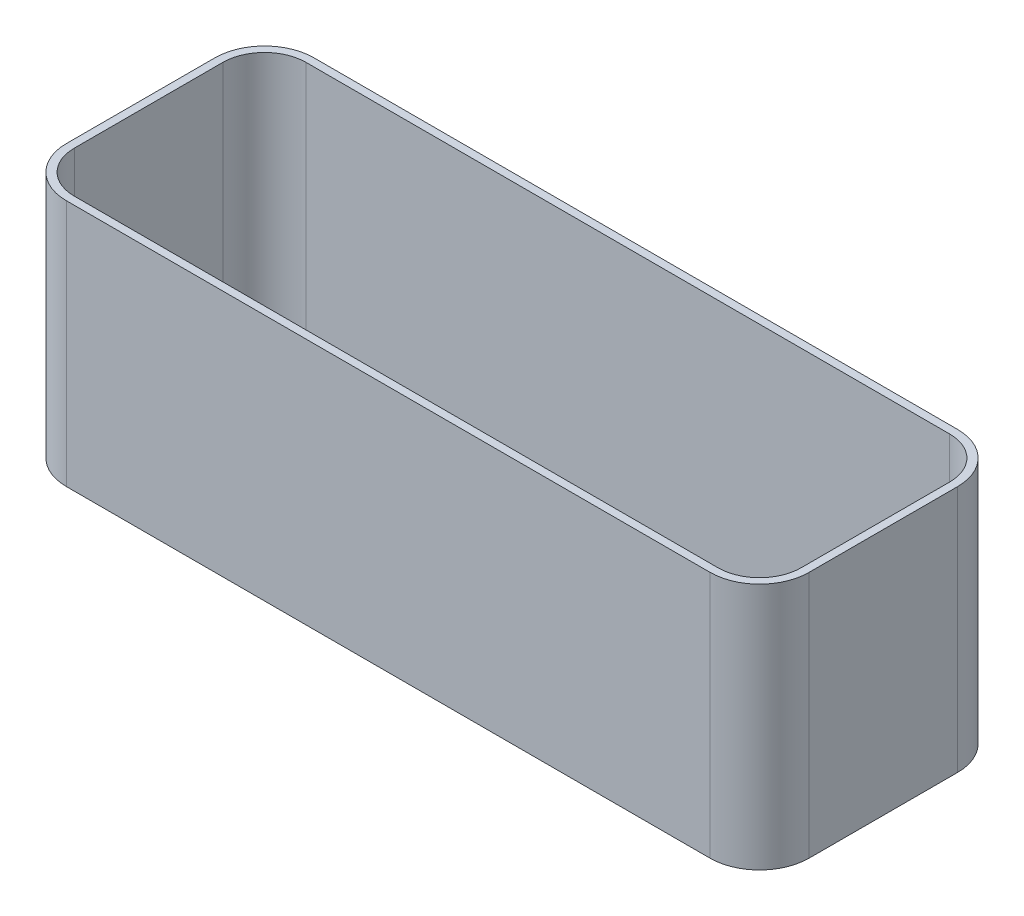
SolidWorks part; units mm, degrees
ref_plane "前视基准面" through (0, 0, 0) normal (0, 0, 1) x (1, 0, 0)
ref_plane "上视基准面" through (0, 0, 0) normal (0, 1, 0) x (1, 0, 0)
ref_plane "右视基准面" through (0, 0, 0) normal (1, 0, 0) x (0, 0, -1)
sketch "草图1" plane through (0, 0, 0) normal (0, 1, 0) x (1, 0, 0)
  line L1 (10, 0) -> (140, 0)
  line L2 (0, 10) -> (0, 40)
  line L3 (10, 50) -> (140, 50)
  line L4 (150, 10) -> (150, 40)
  arc A0 (150, 40) -> (140, 50) centre (140, 40) ccw
  arc A1 (140, 0) -> (150, 10) centre (140, 10) ccw
  arc A2 (10, 0) -> (0, 10) centre (10, 10) cw
  arc A3 (0, 40) -> (10, 50) centre (10, 40) cw
  point P9 (150, 0)
  point P12 (0, 0)
  point P15 (0, 50)
  dimension "D3" = 10
  dimension "D1" = 50
  dimension "D2" = 150
extrude "凸台-拉伸1" add sketch "草图1" along normal blind 50
shell "抽壳1" thickness 1.6
